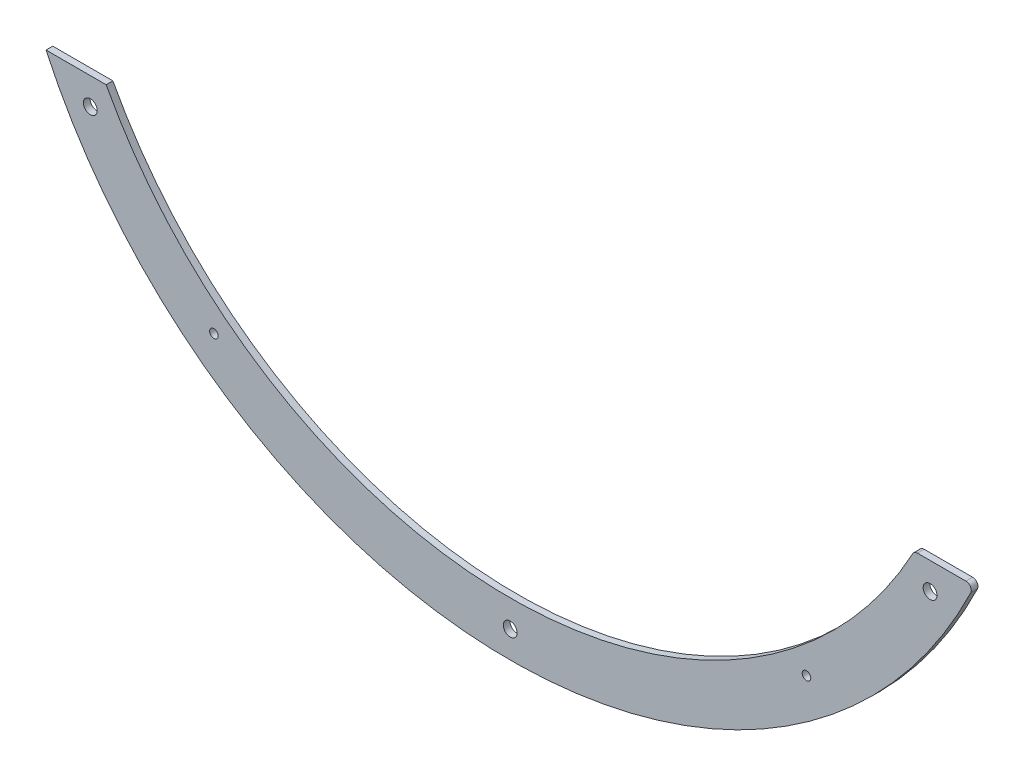
SolidWorks part; units mm, degrees
material "PC High Viscosity"
ref_plane "Front Plane" through (0, 0, 0) normal (0, 0, 1) x (1, 0, 0)
ref_plane "Top Plane" through (0, 0, 0) normal (0, 1, 0) x (1, 0, 0)
ref_plane "Right Plane" through (0, 0, 0) normal (1, 0, 0) x (0, 0, -1)
sketch "Sketch1" plane through (0, 0, 0) normal (0, 0, 1) x (1, 0, 0)
  line L0 (0, 215.9) -> (0, -215.9) construction
  line L1 (-294.6636, -101.6) -> (351.0407, -101.6)
  line L2 (0, -55) -> (0, 55) construction
  line L4 (-218.8678, -101.6) -> (-229.0278, -101.6)
  circle A0 centre (0, 0) radius 241.3
  circle A1 centre (0, 0) radius 215.9
  circle A15 centre (0, -228.6) radius 3.2639
  circle A16 centre (-197.9734, -114.3) radius 3.2639
  circle A17 centre (-197.9734, 114.3) radius 3.2639
  circle A18 centre (0, 228.6) radius 3.2639
  circle A19 centre (197.9734, 114.3) radius 3.2639
  circle A20 centre (197.9734, -114.3) radius 3.2639
  circle A21 centre (-139.7, -177.8) radius 2.0193
  circle A22 centre (139.7, -177.8) radius 2.0193
  point P19 (0, 0)
  point P21 (0, 0)
  point P31 (0, 0)
  dimension "D1" = 482.6
  dimension "D2" = 431.8
  dimension "D3" = 228.6
  dimension "D7" = 177.8
  dimension "D8" = 101.6
  dimension "D4" = 6.5278
  dimension "D6" = 4.0386
  dimension "D9" = 139.7
  dimension "D10" = 10.16
  dimension "D12" = 101.6
  dimension "D5" = 6
extrude "Boss-Extrude1" add sketch "Sketch1" along normal blind 3.175
fillet "Fillet1" radius 2.54 2 edges at (190.5, -101.6, 1.5875) (218.8678, -101.6, 1.5875)
